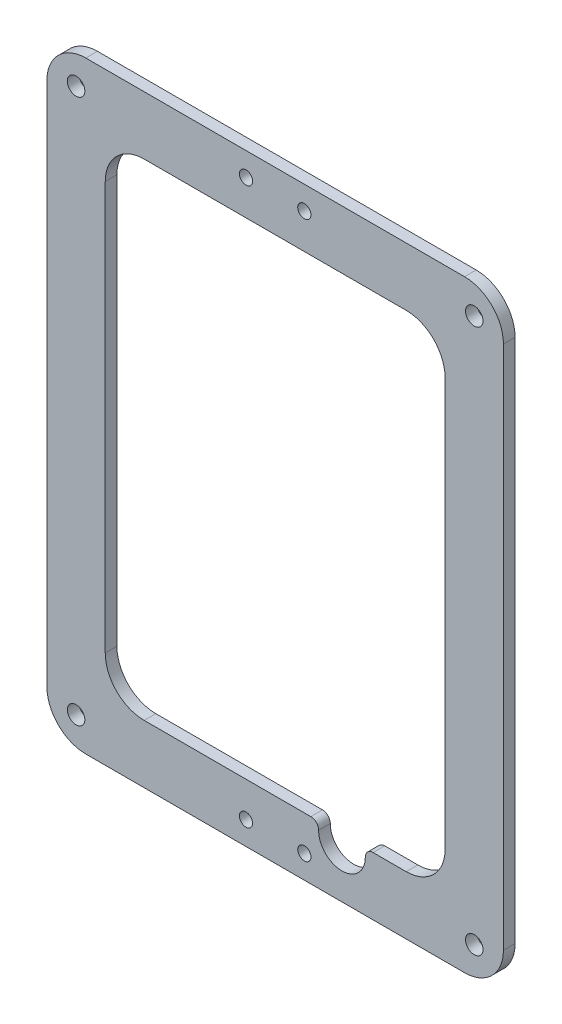
SolidWorks part; units mm, degrees
ref_plane "Plan de face" through (0, 0, 0) normal (0, 0, 1) x (1, 0, 0)
ref_plane "Plan de dessus" through (0, 0, 0) normal (0, 1, 0) x (1, 0, 0)
ref_plane "Plan de droite" through (0, 0, 0) normal (1, 0, 0) x (0, 0, -1)
sketch "Esquisse1" plane through (0, 0, 0) normal (0, 0, 1) x (1, 0, 0)
  line L0 (-43.6965, -25) -> (-43.6965, -130)
  line L1 (-33.6965, -140) -> (33.6965, -140)
  line L2 (43.6965, -130) -> (43.6965, -25)
  line L3 (33.6965, -15) -> (-33.6965, -15)
  line L4 (-58.6965, -10) -> (-58.6965, -145)
  line L5 (-48.6965, -155) -> (48.6965, -155)
  line L6 (58.6965, -145) -> (58.6965, -10)
  line L7 (48.6965, 0) -> (-48.6965, 0)
  line L8 (-58.6965, -10) -> (-58.6965, -145)
  line L9 (-48.6965, -155) -> (48.6965, -155)
  line L10 (58.6965, -145) -> (58.6965, -10)
  line L11 (48.6965, 0) -> (-48.6965, 0)
  line L12 (43.6965, -15) -> (-43.6965, -15) construction
  line L13 (-43.6965, -15) -> (-43.6965, -140) construction
  line L14 (-43.6965, -140) -> (43.6965, -140) construction
  line L15 (43.6965, -140) -> (43.6965, -15) construction
  line L30 (-58.6965, -10) -> (-43.6965, -5) construction
  line L31 (0, 0) -> (0, -155) construction
  line L32 (58.6965, -77.5) -> (-58.6965, -77.5) construction
  arc A4 (-48.6965, 0) -> (-58.6965, -10) centre (-48.6965, -10) ccw
  arc A5 (-58.6965, -145) -> (-48.6965, -155) centre (-48.6965, -145) ccw
  arc A6 (48.6965, -155) -> (58.6965, -145) centre (48.6965, -145) ccw
  arc A7 (58.6965, -10) -> (48.6965, 0) centre (48.6965, -10) ccw
  arc A8 (-48.6965, 0) -> (-58.6965, -10) centre (-48.6965, -10) ccw
  arc A9 (-58.6965, -145) -> (-48.6965, -155) centre (-48.6965, -145) ccw
  arc A10 (48.6965, -155) -> (58.6965, -145) centre (48.6965, -145) ccw
  arc A11 (58.6965, -10) -> (48.6965, 0) centre (48.6965, -10) ccw
  arc A12 (-33.6965, -15) -> (-43.6965, -25) centre (-33.6965, -25) ccw
  arc A13 (-43.6965, -15) -> (-43.6965, -15) centre (-43.6965, -15) ccw construction
  arc A14 (-43.6965, -130) -> (-33.6965, -140) centre (-33.6965, -130) ccw
  arc A15 (-43.6965, -140) -> (-43.6965, -140) centre (-43.6965, -140) ccw construction
  arc A16 (33.6965, -140) -> (43.6965, -130) centre (33.6965, -130) ccw
  arc A17 (43.6965, -140) -> (43.6965, -140) centre (43.6965, -140) ccw construction
  arc A18 (43.6965, -25) -> (33.6965, -15) centre (33.6965, -25) ccw
  arc A19 (43.6965, -15) -> (43.6965, -15) centre (43.6965, -15) ccw construction
  circle A20 centre (17.175, -142.0947) radius 9 construction
  circle A21 centre (17.175, -142.0947) radius 9 construction
  circle A22 centre (17.175, -142.0947) radius 6
  point P40 (-51.1965, -7.5)
  point P41 (51.1965, -147.5)
  point P46 (51.1965, -7.5)
  point P48 (-51.1965, -147.5)
  dimension "D3" = 10
  dimension "D4" = 12
  dimension "D1" = 0
  dimension "D2" = 15
extrude "Boss.-Extru.1" add sketch "Esquisse1" along normal blind 3 from offset 100 contours L10 A11 L11 A8 L8 A9 L9 A10 A21 L1 A14 L0 A12 L3 A18 L2 A16
hole_wizard "Dégagement M41" positions "Esquisse2" profile "Esquisse3" hole size "M4" standard "ISO" end condition through all
sketch "Esquisse2" plane through (0, 0, 103) normal (0, 0, 1) x (1, 0, 0)
  point P0 (-51.1965, -7.5)
  point P3 (51.1965, -7.5)
  point P6 (51.1965, -147.5)
  point P9 (-51.1965, -147.5)
sketch "Esquisse3" plane through (-51.1965, -7.5, 103) normal (1, 0, 0) x (0, -1, 0)
  line L0 (0, 0) -> (0, 3)
  line L1 (0, 3) -> (2.25, 3)
  line L2 (2.25, 3) -> (2.25, 0)
  line L5 (2.25, 0) -> (0, 0)
  line L11 (0, -6.35) -> (0, 107.95) construction
  dimension "Diamètre du perçage jusqu'au prochain" = 4.5
  dimension "Profondeur du perçage jusqu'au prochain" = 3
fillet "Congé1" radius 2 2 edges at (11.5525, -140, 101.5) (22.7975, -140, 101.5)
sketch "Esquisse4" plane through (0, 0, 103) normal (0, 0, 1) x (1, 0, 0)
  line L0 (0, 0) -> (0, -155) construction
  line L1 (-48.6965, -155) -> (48.6965, -155) construction
  line L2 (7.5, -149) -> (-7.5, -149) construction
  line L3 (-7.5, -6) -> (7.5, -6) construction
  point P5 (0, -6)
  point P6 (0, -149)
  point P9 (0, -6)
  point P10 (0, -149)
  dimension "D1" = 6
  dimension "D2" = 6
  dimension "D3" = 15
hole_wizard "Dégagement M31" positions "Esquisse5" profile "Esquisse6" hole size "M3" standard "ISO" end condition through all
sketch "Esquisse5" plane through (0, 0, 103) normal (0, 0, 1) x (1, 0, 0)
  point P0 (-7.5, -6)
  point P3 (7.5, -6)
  point P6 (-7.5, -149)
  point P9 (7.5, -149)
sketch "Esquisse6" plane through (-7.5, -6, 103) normal (1, 0, 0) x (0, -1, 0)
  line L0 (0, 0) -> (0, 3)
  line L1 (0, 3) -> (1.7, 3)
  line L2 (1.7, 3) -> (1.7, 0)
  line L5 (1.7, 0) -> (0, 0)
  line L11 (0, -6.35) -> (0, 107.95) construction
  dimension "Diamètre du perçage jusqu'au prochain" = 3.4
  dimension "Profondeur du perçage jusqu'au prochain" = 3
